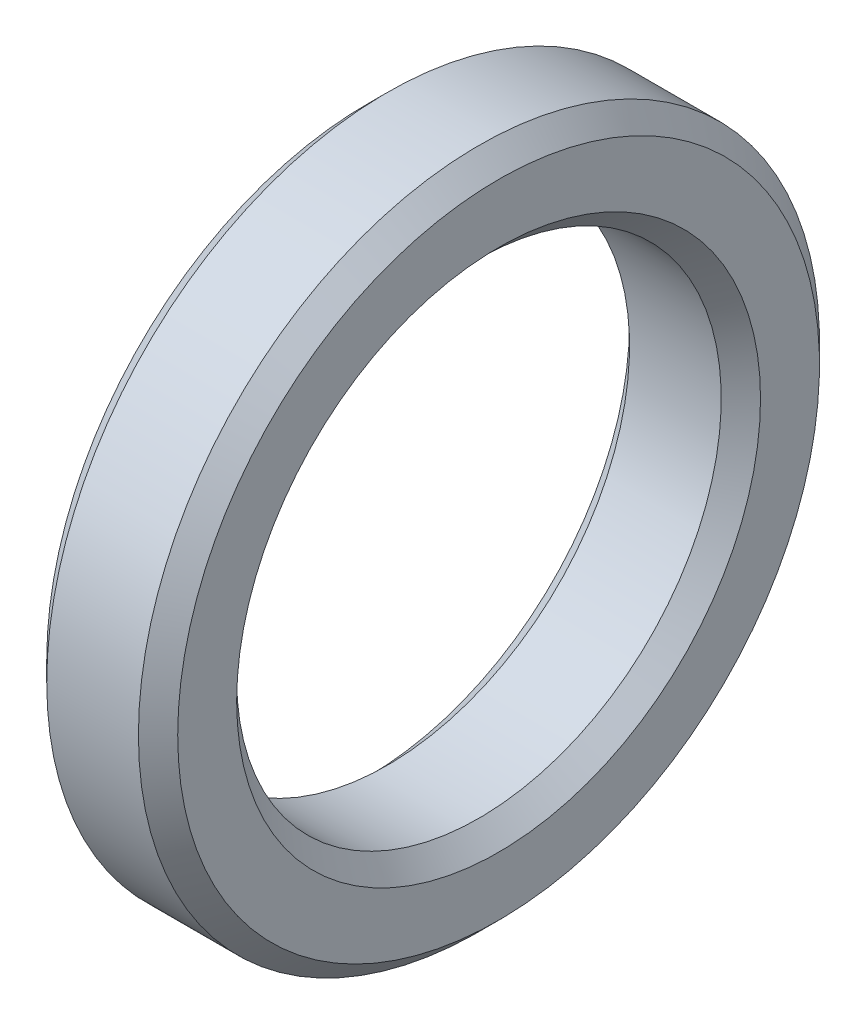
SolidWorks part; units mm, degrees
ref_plane "Спереди" through (0, 0, 0) normal (0, 0, 1) x (1, 0, 0)
ref_plane "Сверху" through (0, 0, 0) normal (0, 1, 0) x (1, 0, 0)
ref_plane "Справа" through (0, 0, 0) normal (1, 0, 0) x (0, 0, -1)
other "Configuration Table"
sketch "Эскиз1" plane through (0, 0, 0) normal (0, 0, 1) x (1, 0, 0)
  line L0 (1.5, 18.5) -> (8.5, 18.5)
  line L1 (10, 20) -> (10, 24.5)
  line L2 (8.5, 26) -> (1.5, 26)
  line L3 (0, 24.5) -> (0, 20)
  line L4 (0, 0) -> (23.507, 0) construction
  line L5 (0, 0) -> (0, 30.2935) construction
  line L6 (0, 20) -> (1.5, 18.5)
  line L7 (8.5, 18.5) -> (10, 20)
  line L8 (10, 24.5) -> (8.5, 26)
  line L9 (1.5, 26) -> (0, 24.5)
  point P0 (0, 18.5)
  point P1 (10, 18.5)
  point P3 (10, 26)
  point P4 (0, 26)
  dimension "D1" = 37
  dimension "D2" = 10
  dimension "D3" = 52
revolve "Повернуть1" add sketch "Эскиз1" angle 360 about L4
cosmetic thread "Условное изображение резьбы1" parameters "D1"=5, "D2"=46.344
sketch "Эскиз11" plane through (0, 0, 0) normal (-1, 0, 0) x (0, 0, 1)
  line L0 (0, 0) -> (0, 33.464) construction
  line L1 (0, 0) -> (32.327, 0) construction
  circle A0 centre (0, 0) radius 22
  point P7 (0, 22)
  point P9 (22, 0)
  point P11 (0, -22)
  point P13 (-22, 0)
  dimension "D1" = 44
hole_wizard "Отверстия под штифты Ø4.0 мм2" positions "Эскиз11" profile "Эскиз12" hole size "Ø4.0" standard "DIN"
sketch "Эскиз12" plane through (0, 0, -22) normal (0, 1, 0) x (0, 0, 1)
  line L0 (0, 0) -> (0, 6.2017)
  line L1 (0, 6.2017) -> (2, 5)
  line L2 (2, 5) -> (2, 0)
  line L5 (2, 0) -> (0, 0)
  line L10 (0, 6.2017) -> (-2, 5) construction
  line L11 (0, -6.35) -> (0, 107.95) construction
  dimension "Диаметр отверстия" = 4
  dimension "Глубина отверстия" = 5
  dimension "Угол заточки сверла" = 118
